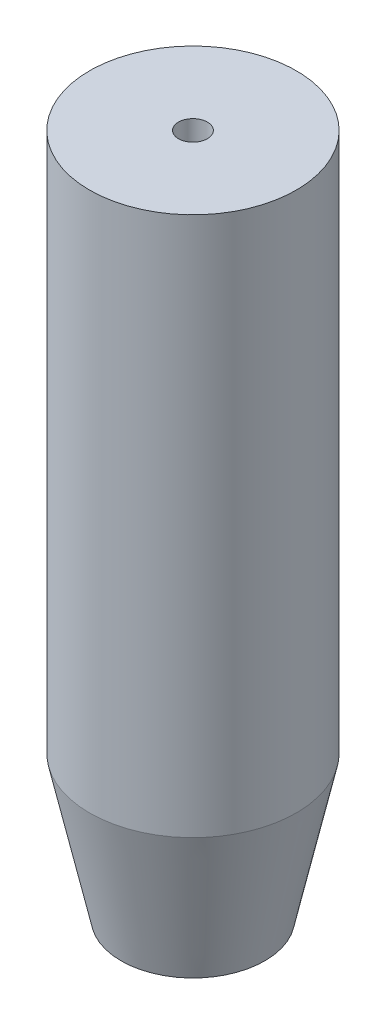
SolidWorks part; units mm, degrees
material "6061-T6 (SS)"
ref_plane "Front Plane" through (0, 0, 0) normal (0, 0, 1) x (1, 0, 0)
ref_plane "Top Plane" through (0, 0, 0) normal (0, 1, 0) x (1, 0, 0)
ref_plane "Right Plane" through (0, 0, 0) normal (1, 0, 0) x (0, 0, -1)
sketch "Sketch1" plane through (0, 0, 0) normal (0, 1, 0) x (1, 0, 0)
  circle A0 centre (0, 0) radius 18.2562
  dimension "D1" = 36.5125
extrude "Boss-Extrude1" add sketch "Sketch1" along normal blind 120.65
chamfer "Chamfer1" distance 5.5562 distance2 25.4 1 edges at (0, 0, 18.2562)
hole_wizard "1/4-20 Tapped Hole1" positions "Sketch2" profile "Sketch3" tap size "1/4-20" standard "ANSI Inch"
sketch "Sketch2" plane through (0, 120.65, 0) normal (0, 1, 0) x (1, 0, 0)
  point P0 (0, 0)
sketch "Sketch3" plane through (0, 120.65, 0) normal (1, 0, 0) x (0, 0, 1)
  line L0 (0, 0) -> (0, 18.0438)
  line L1 (0, 18.0438) -> (2.5527, 16.51)
  line L2 (2.5527, 16.51) -> (2.5527, 0)
  line L5 (2.5527, 0) -> (0, 0)
  line L10 (0, 18.0438) -> (-2.5527, 16.51) construction
  line L11 (0, -6.35) -> (0, 107.95) construction
  dimension "Tap Drill Dia." = 5.1054
  dimension "Tap Drill Depth" = 16.51
  dimension "Drill Angle" = 118
cosmetic thread "Hole Thread1"
